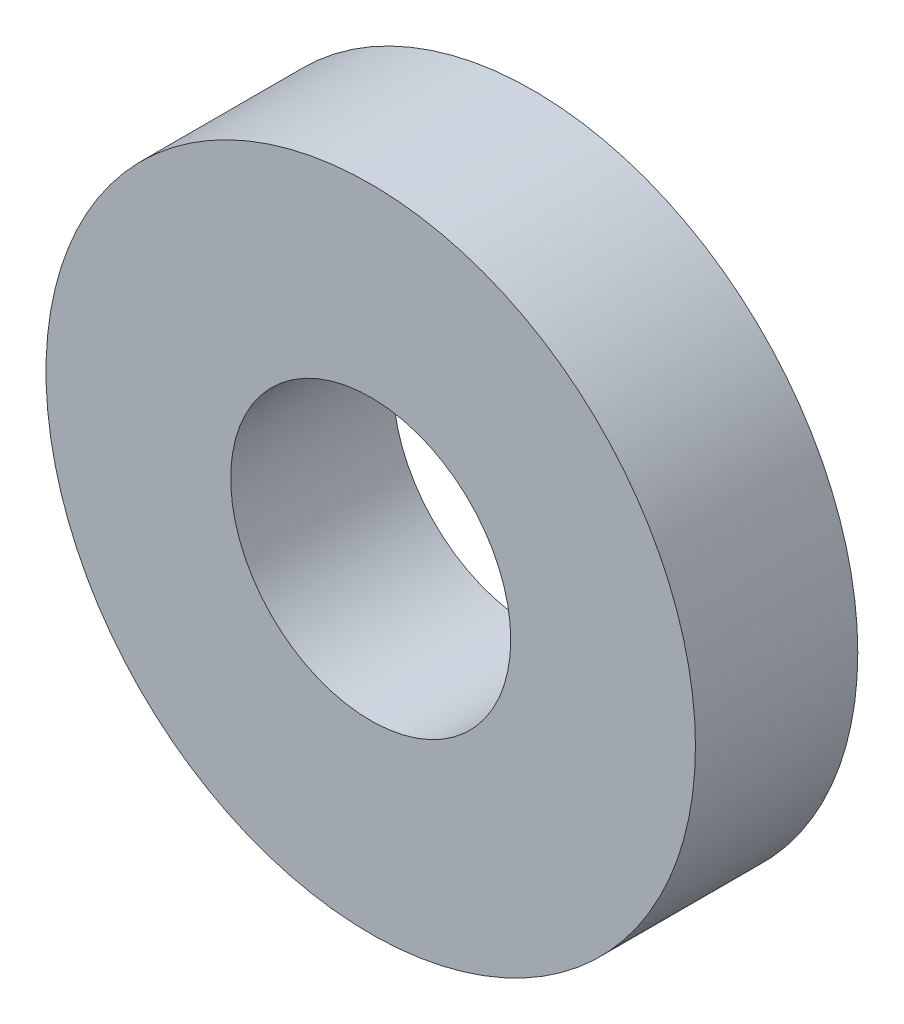
SolidWorks part; units mm, degrees
material "ABS"
ref_plane "Front Plane" through (0, 0, 0) normal (0, 0, 1) x (1, 0, 0)
ref_plane "Top Plane" through (0, 0, 0) normal (0, 1, 0) x (1, 0, 0)
ref_plane "Right Plane" through (0, 0, 0) normal (1, 0, 0) x (0, 0, -1)
sketch "Sketch1" plane through (0, 0, 0) normal (0, 0, 1) x (1, 0, 0)
  circle A0 centre (0, 0) radius 4
  circle A1 centre (0, 0) radius 1.725
  dimension "D1" = 3.45
  dimension "D2" = 8
extrude "Main Spacer" add sketch "Sketch1" along normal blind 2
equation "\"D1@Sketch1\"=3.00mm+\"print_free@Parameters@RobotHandParameters.SLDPRT\""
